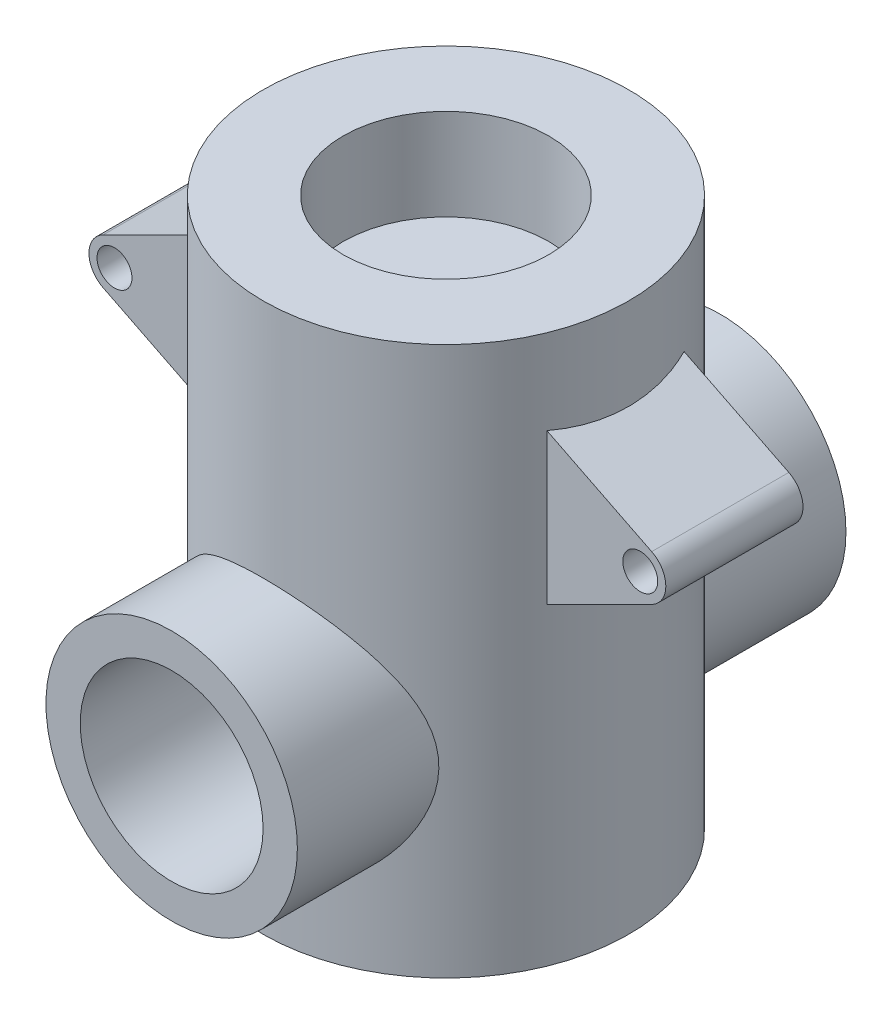
SolidWorks part; units mm, degrees
ref_plane "Plane1" through (0, 0, 0) normal (0, 0, 1) x (1, 0, 0)
ref_plane "Plane2" through (0, 0, 0) normal (0, 1, 0) x (1, 0, 0)
ref_plane "Plane3" through (0, 0, 0) normal (1, 0, 0) x (0, 0, -1)
other "Configuration Table"
sketch "Sketch1" plane through (0, 0, 0) normal (0, 0, 1) x (1, 0, 0)
  line L0 (40, 10) -> (0, 10)
  line L1 (0, 10) -> (0, -110)
  line L2 (40, 10) -> (40, -110)
  line L3 (0, -110) -> (40, -110)
  line L12 (0, 300) -> (0, -100) construction
  dimension "D1" = 120
  dimension "D2" = 40
  dimension "D3" = 10
revolve "Base-Revolve" add sketch "Sketch1" angle 360 about L12
sketch "Sketch2" plane through (0, 0, 0) normal (0, 0, 1) x (1, 0, 0)
  line L0 (0, 300) -> (0, -100) construction
  circle A0 centre (0, -70) radius 20
  dimension "D2" = 40
sketch "Sketch3" plane through (0, 0, 0) normal (0, 0, 1) x (1, 0, 0)
  line L0 (30, -5) -> (60, -20)
  line L1 (30, -45) -> (60, -30)
  line L2 (30, -5) -> (30, -45)
  arc A0 (60, -30) -> (60, -20) centre (57.5, -25) ccw
  circle A1 centre (57.5, -25) radius 3.8212
  dimension "D2" = 5.5902
  dimension "D3" = 7.6423
  dimension "D1" = 40
  dimension "D4" = 27.5
extrude "Boss-Extrude1" add sketch "Sketch3" along normal mid plane 30
mirror "Mirror1" about plane through (0, 0, 0) normal (1, 0, 0) of "Boss-Extrude1"
sketch "Sketch5" plane through (0, 0, 0) normal (0, 0, 1) x (1, 0, 0)
  line L0 (0, 300) -> (0, -100) construction
  line L1 (40, -110) -> (-40, -110) construction
  circle A0 centre (0, -70) radius 27.5
  dimension "D1" = 55
  dimension "D2" = 40
extrude "Boss-Extrude2" add sketch "Sketch5" along normal mid plane 120
sketch "Sketch4" plane through (0, 10, 0) normal (0, 1, 0) x (-1, 0, 0)
  circle A0 centre (0, 0) radius 22.5
  dimension "D1" = 45
extrude "Cut-Extrude2" cut sketch "Sketch4" against normal blind 20
extrude "Cut-Extrude3" cut sketch "Sketch2" against normal through all and the other way through all
